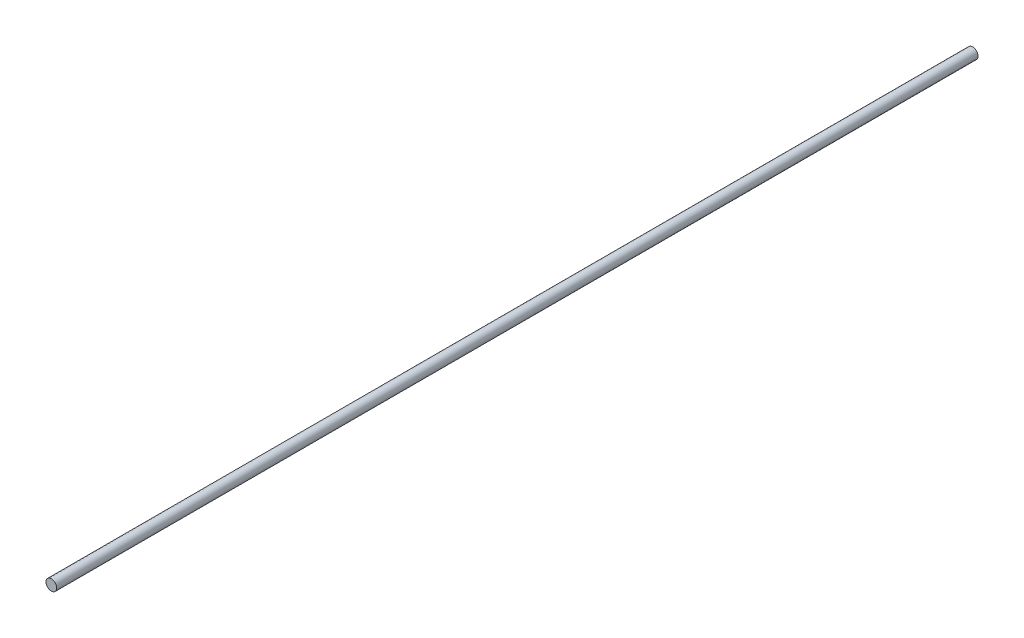
SolidWorks part; units mm, degrees
ref_plane "Plan de face" through (0, 0, 0) normal (0, 0, 1) x (1, 0, 0)
ref_plane "Plan de dessus" through (0, 0, 0) normal (0, 1, 0) x (1, 0, 0)
ref_plane "Plan de droite" through (0, 0, 0) normal (1, 0, 0) x (0, 0, -1)
sketch "Esquisse1" plane through (0, 0, 0) normal (0, 0, 1) x (1, 0, 0)
  circle A0 centre (0, 0) radius 4
  dimension "D1" = 8
extrude "Boss.-Extru.1" add sketch "Esquisse1" along normal blind 688
